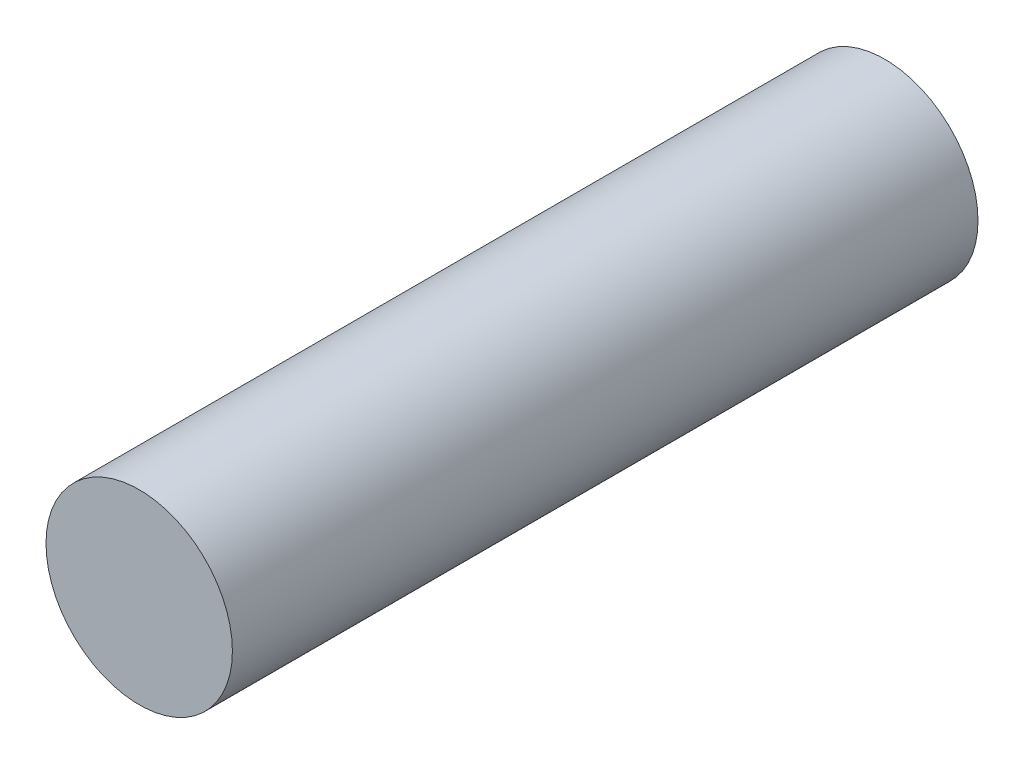
SolidWorks part; units mm, degrees
ref_plane "Front Plane" through (0, 0, 0) normal (0, 0, 1) x (1, 0, 0)
ref_plane "Top Plane" through (0, 0, 0) normal (0, 1, 0) x (1, 0, 0)
ref_plane "Right Plane" through (0, 0, 0) normal (1, 0, 0) x (0, 0, -1)
sketch "Sketch2" plane through (0, 0, 0) normal (0, 0, 1) x (1, 0, 0)
  circle A0 centre (0, 0) radius 1.5
  dimension "D1" = 3
extrude "Boss-Extrude1" add sketch "Sketch2" along normal blind 12
